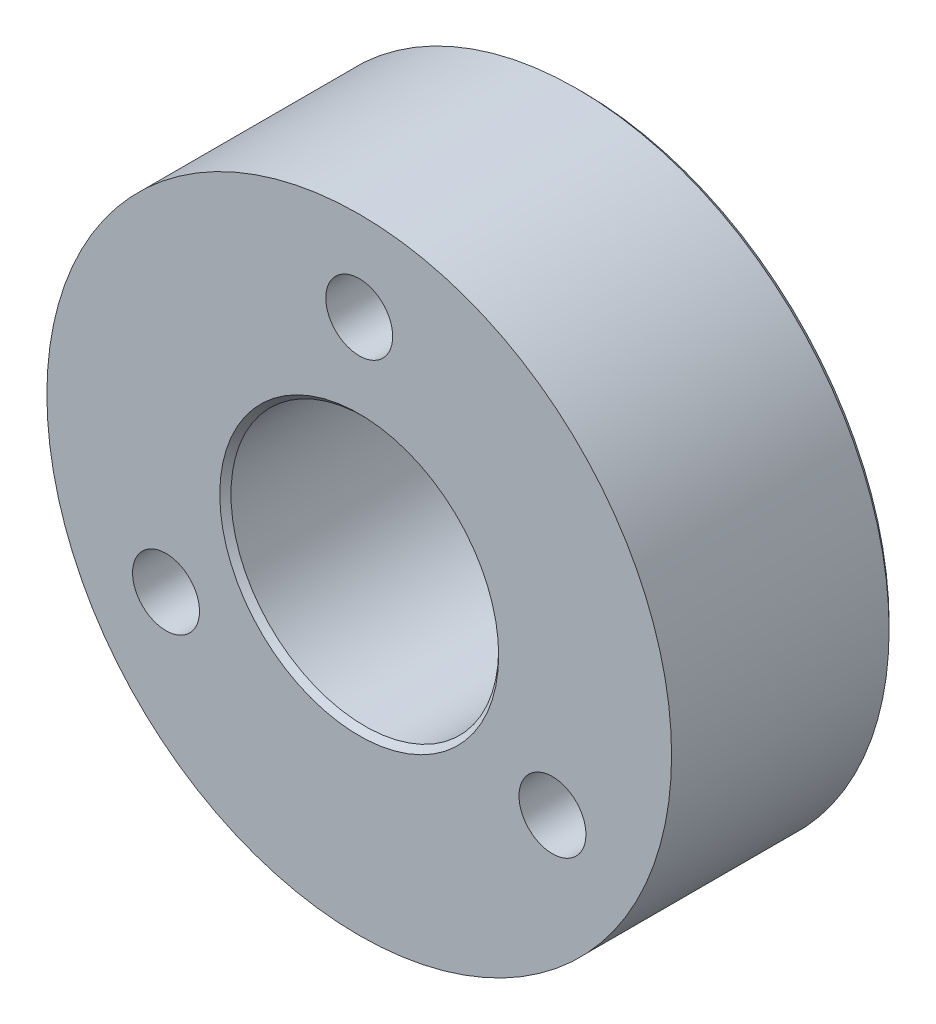
SolidWorks part; units mm, degrees
ref_plane "Front Plane" through (0, 0, 0) normal (0, 0, 1) x (1, 0, 0)
ref_plane "Top Plane" through (0, 0, 0) normal (0, 1, 0) x (1, 0, 0)
ref_plane "Right Plane" through (0, 0, 0) normal (1, 0, 0) x (0, 0, -1)
sketch "Sketch2" plane through (0, 0, 0) normal (0, 0, 1) x (1, 0, 0)
  circle A0 centre (0, 0) radius 14
  circle A1 centre (0, 0) radius 6
  circle A2 centre (0, 0) radius 10 construction
  circle A3 centre (0, 10) radius 1.5
  circle A4 centre (8.6603, -5) radius 1.5
  circle A5 centre (-8.6603, -5) radius 1.5
  point P14 (0, 0)
  dimension "D1" = 28
  dimension "D2" = 12
  dimension "D3" = 20
  dimension "D4" = 3
  dimension "D5" = 3
extrude "Boss-Extrude1" add sketch "Sketch2" along normal blind 10
chamfer "Chamfer1" distance 0.25 angle 45 6 edges at (6, 0, 10) (-7.1603, -5, 0) (10.1603, -5, 0) (1.5, 10, 0) (6, 0, 0) (14, 0, 0)
